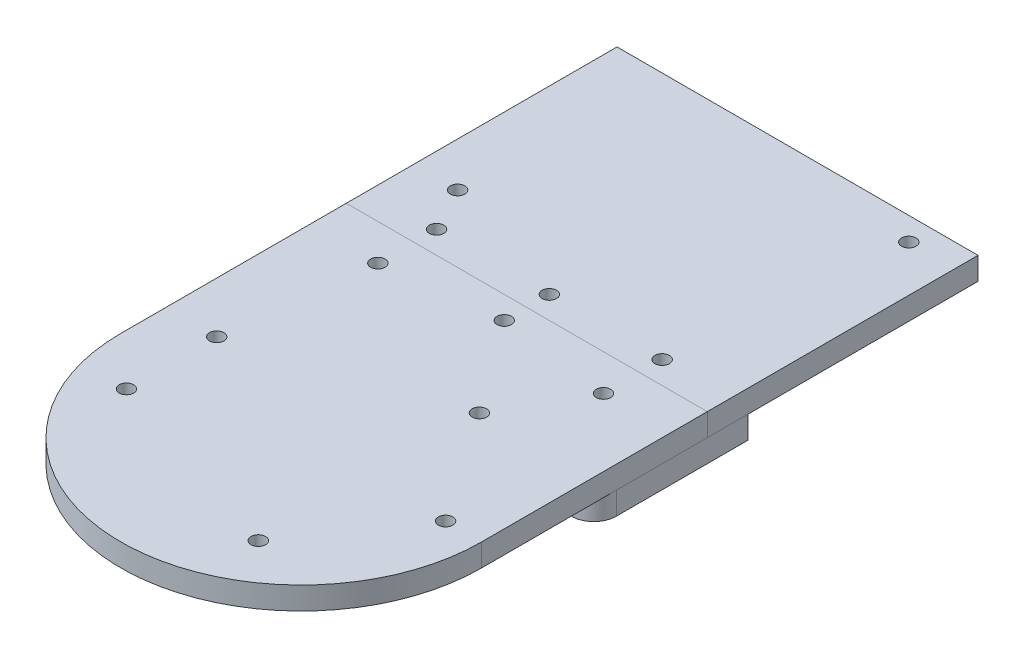
SolidWorks part; units mm, degrees
ref_plane "前视基准面" through (0, 0, 0) normal (0, 0, 1) x (1, 0, 0)
ref_plane "上视基准面" through (0, 0, 0) normal (0, 1, 0) x (1, 0, 0)
ref_plane "右视基准面" through (0, 0, 0) normal (1, 0, 0) x (0, 0, -1)
sketch "草图1" plane through (0, 0, 0) normal (0, 1, 0) x (1, 0, 0)
  line L2 (-40, 0) -> (-40, 110)
  line L3 (-40, 110) -> (40, 110)
  line L4 (40, 0) -> (40, 110)
  arc A0 (-40, 0) -> (40, 0) centre (0, 0) ccw
  dimension "D1" = 80
  dimension "D2" = 110
extrude "凸台-拉伸1" add sketch "草图1" along normal blind 5
sketch "草图2" plane through (0, 5, 0) normal (0, 1, 0) x (1, 0, 0)
  line L0 (0, 0) -> (52.0944, 0) construction
  circle A2 centre (15, 24.5) radius 1.6
  circle A3 centre (15, -24.5) radius 1.6
  dimension "D1" = 49
  dimension "D2" = 15
  dimension "D3" = 3.2
extrude "切除-拉伸1" cut sketch "草图2" against normal blind 10
sketch "草图3" plane through (0, 0, 0) normal (0, -1, 0) x (1, 0, 0)
  line L2 (-45.9136, 0) -> (2.1968, 0) construction
  circle A0 centre (0, 0) radius 32 construction
  circle A1 centre (-32, 0) radius 1.6 construction
  circle A2 centre (32, 0) radius 1.6
  circle A3 centre (-28.725, 10) radius 1.6
  circle A4 centre (-28.725, -10) radius 1.6
  dimension "D1" = 64
  dimension "D2" = 3.2
  dimension "D3" = 20
  dimension "D4" = 28.725
extrude "切除-拉伸2" cut sketch "草图3" against normal blind 10
sketch "草图4" plane through (0, 5, 0) normal (0, 1, 0) x (1, 0, 0)
  line L0 (-30.218, 64.879) -> (29.782, 104.879) construction
  line L1 (-54.3844, 85) -> (52.2008, 85) construction
  line L2 (0, 110) -> (0, 49.808) construction
  line L3 (40, 0) -> (40, 110) construction
  line L4 (40, 110) -> (-40, 110) construction
  line L5 (-40, 110) -> (-40, 0) construction
  circle A0 centre (29.782, 104.879) radius 1.6
  circle A1 centre (-30.218, 64.879) radius 1.6
  circle A2 centre (36, 108) radius 1.6 construction
  circle A6 centre (36, 62) radius 1.6 construction
  circle A7 centre (-36, 62) radius 1.6 construction
  circle A8 centre (-36, 108) radius 1.6 construction
  dimension "D1" = 4
  dimension "D3" = 3.2
  dimension "D5" = 10.218
  dimension "D6" = 5.121
  dimension "D7" = 9.782
  dimension "D8" = 45.121
  dimension "D2" = 2
  dimension "D4" = 25
extrude "切除-拉伸3" cut sketch "草图4" against normal blind 10
ref_plane "基准面1" through (0, 0, -50) normal (0, 0, -1) x (-1, 0, 0)
split "分割1" trim tools "基准面1" bodies to split 109 resulting bodies 110 111
sketch "草图5" plane through (0, 0, 0) normal (0, -1, 0) x (1, 0, 0)
  line L0 (0, 0) -> (0, -65.9342) construction
  line L1 (-40, -50) -> (40, -50) construction
  circle A3 centre (25, -55) radius 1.6
  circle A4 centre (0, -55) radius 1.6
  circle A5 centre (-25, -55) radius 1.6
  circle A6 centre (0, -45) radius 1.6
  circle A7 centre (-25, -42) radius 1.6
  circle A8 centre (25, -42) radius 1.6
  dimension "D1" = 5
  dimension "D2" = 50
  dimension "D3" = 3.2
  dimension "D4" = 5
  dimension "D5" = 8
extrude "切除-拉伸4" cut sketch "草图5" against normal through all and the other way through all
sketch "草图6" plane through (0, 0, 0) normal (0, -1, 0) x (1, 0, 0)
  line L0 (-40, -50) -> (-40, 0) construction
  line L2 (-40, -9) -> (-40, -59)
  line L3 (-40, -59) -> (40, -59)
  line L4 (40, -9) -> (40, -59)
  line L5 (40, -50) -> (40, -110) construction
  line L6 (40, -110) -> (-40, -110) construction
  line L7 (40, 0) -> (40, -50) construction
  arc A0 (-40, -9) -> (40, -9) centre (0, 0) ccw
  arc A1 (40, -9) -> (-40, -9) centre (0, 0) ccw construction
  dimension "D2" = 82
  dimension "D1" = 51
extrude "凸台-拉伸2" add sketch "草图6" along normal blind 5 separate body
fillet "圆角1" radius 5 2 edges at (40, -2.5, -9) (-40, -2.5, -9)
sketch "草图7" plane through (0, 5, 0) normal (0, 1, 0) x (1, 0, 0)
  circle A12 centre (25, 42) radius 1.6 construction
  circle A13 centre (25, 55) radius 1.6 construction
  circle A14 centre (0, 45) radius 1.6 construction
  circle A15 centre (0, 55) radius 1.6 construction
  circle A16 centre (-25, 42) radius 1.6 construction
  circle A17 centre (-25, 55) radius 1.6 construction
  circle A18 centre (25, 42) radius 1.6
  circle A19 centre (25, 55) radius 1.6
  circle A20 centre (0, 45) radius 1.6
  circle A21 centre (0, 55) radius 1.6
  circle A22 centre (-25, 42) radius 1.6
  circle A23 centre (-25, 55) radius 1.6
extrude "切除-拉伸5" cut sketch "草图7" against normal blind 39
